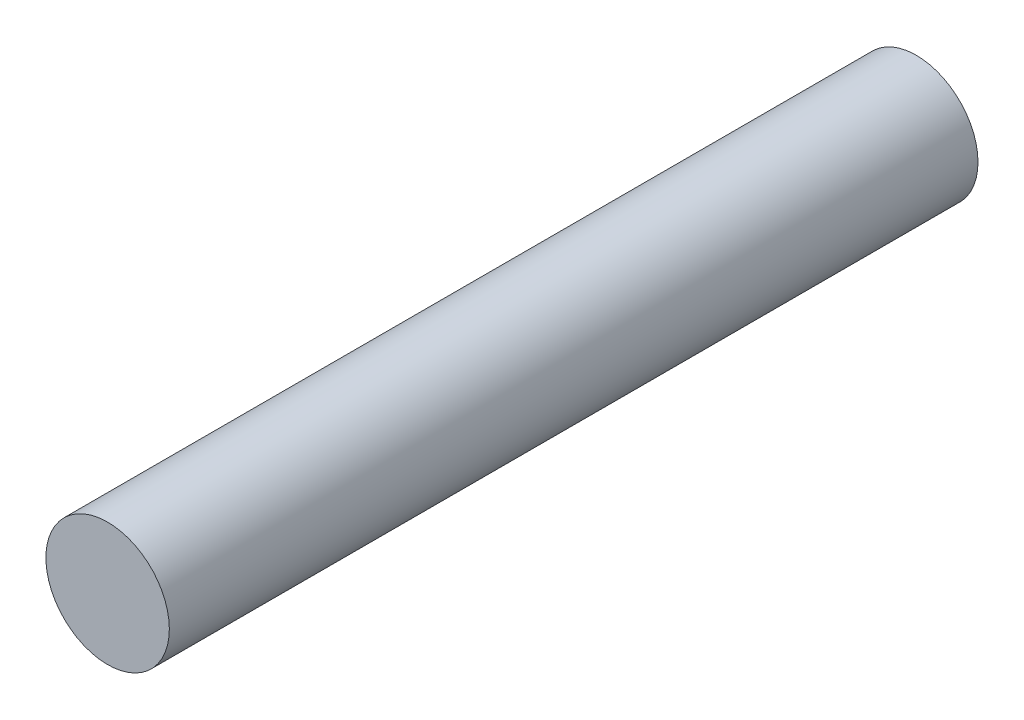
SolidWorks part; units mm, degrees
ref_plane "Alzado" through (0, 0, 0) normal (0, 0, 1) x (1, 0, 0)
ref_plane "Planta" through (0, 0, 0) normal (0, 1, 0) x (1, 0, 0)
ref_plane "Vista lateral" through (0, 0, 0) normal (1, 0, 0) x (0, 0, -1)
sketch "Croquis1" plane through (0, 0, 0) normal (0, 0, 1) x (1, 0, 0)
  circle A0 centre (0, 0) radius 10
extrude "Saliente-Extruir1" add sketch "Croquis1" along normal blind 131
sketch "Croquis2" plane through (0, 0, 131) normal (0, 0, 1) x (1, 0, 0)
  line L0 (0, 0) -> (0, 10) construction
  circle A0 centre (0, 0) radius 10 construction
